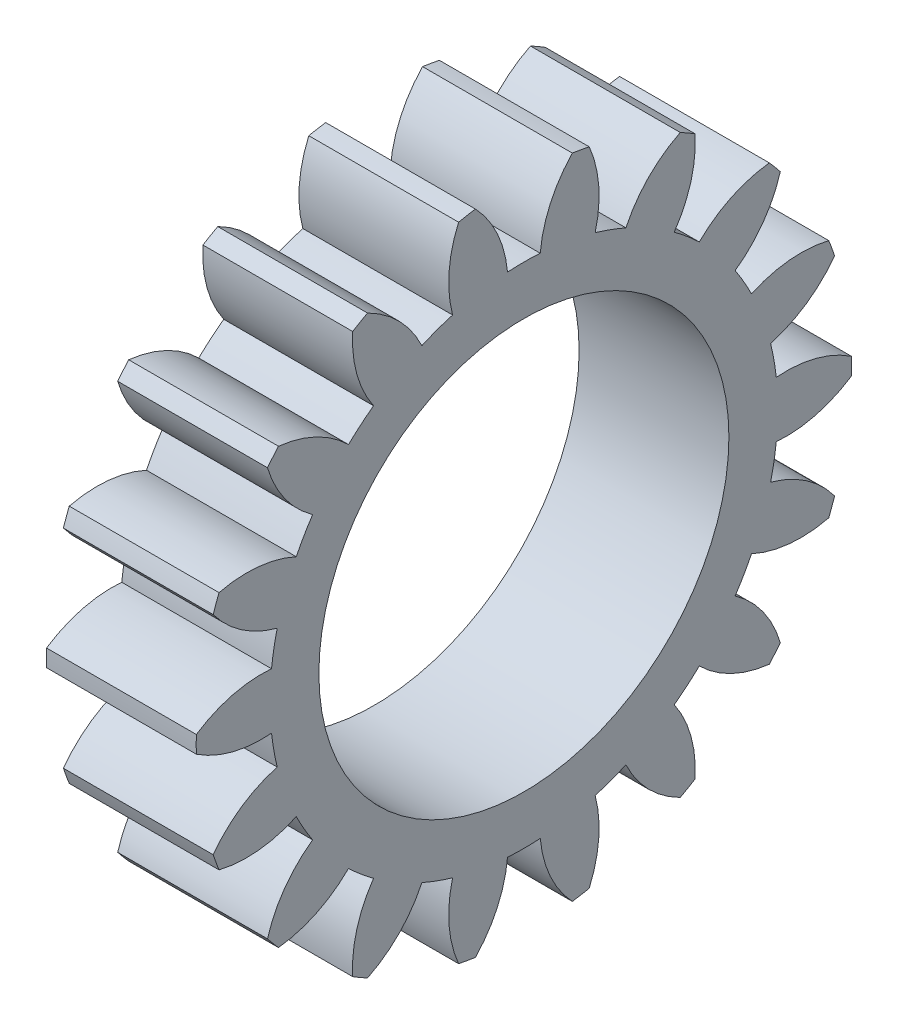
SolidWorks part; units mm, degrees
material "PLA personnalisé"
ref_plane "Plane1" through (0, 0, 0) normal (0, 0, 1) x (1, 0, 0)
ref_plane "Plane2" through (0, 0, 0) normal (0, 1, 0) x (1, 0, 0)
ref_plane "Plane3" through (0, 0, 0) normal (1, 0, 0) x (0, 0, -1)
other "Configuration Table"
sketch "HoldingSke" plane through (0, 0, 0) normal (0, 1, 0) x (1, 0, 0)
  line L0 (0, 0) -> (0.5435, -0.1766)
  line L1 (-15, 0) -> (100, 0) construction
  line L2 (0, 0) -> (-2.1039, 2.3779)
  line L3 (0, 0) -> (-11.863, 4.5341)
  line L4 (0, 0) -> (8.2133, 2.6687)
  line L5 (0, 0) -> (-46.8476, -17.4728)
  line L6 (0, 0) -> (-6.6317, -4.4744)
  line L7 (-2.1039, 2.3779) -> (8.6586, 51.2059)
  line L8 (-76.2, 54.61) -> (-74.8, 54.61)
  line L9 (-71.009, 38.7566) -> (-53.1078, 45.2721)
  line L10 (-76.2, 71.12) -> (104.1128, 71.12)
  line L11 (0, 0) -> (-8, 0)
  line L12 (-76.2, 101.6) -> (-76.147, 101.6)
  line L13 (24.9733, 27.94) -> (52.9518, 28.4284)
  line L14 (24.9733, 27.94) -> (24.9743, 27.94)
  line L15 (24.9733, 27.94) -> (100.4006, 29.5858)
  line L16 (-63.627, -1.75) -> (-12.827, -1.75)
  circle A0 centre (0, 0) radius 4
  circle A1 centre (0, 0) radius 13.5615
  circle A2 centre (0, 0) radius 37.5
  circle A3 centre (0, 0) radius 4
  dimension "MHD" = 27.123
  dimension "Hub_dia" = 75
  dimension "Bore" = 8
  dimension "MBD" = 8
  dimension "Num_teeth" = 18
  dimension "Pitch" = 0.5714
  dimension "Overall_len" = 50
  dimension "Show_teeth" = 18
  dimension "Thickness" = 8
  dimension "OAL" = 50.0001
  dimension "T_dim" = 1.4
  dimension "Ap" = 20
  dimension "H" = 19.05
  dimension "Pitch_radius" = 180.3128
  dimension "Width" = 8
  dimension "Backlash" = 0.053
  dimension "Addendum_fac" = 1
  dimension "Dedendum_fac" = 1.25
  dimension "Clearance_fac" = 0.25
  dimension "Dedendum_add" = 0.001
  dimension "Module" = 1.75
sketch "BasProSke" plane through (0, 0, 0) normal (0, 1, 0) x (1, 0, 0)
  line L0 (-10, 0) -> (60, 0) construction
  line L1 (0, 0) -> (0, 17.5)
  line L2 (0, 0) -> (8, 0)
  line L3 (8, 0) -> (8, 17.5)
  line L4 (8, 17.5) -> (0, 17.5)
  dimension "Thickness" = 8
  dimension "Diameter" = 35
revolve "Base-Revolve" add sketch "BasProSke" angle 360 about L0
sketch "TooCutSke" plane through (0, 0, 0) normal (1, 0, 0) x (0, 0, -1)
  line L1 (0, 0) -> (0, 107) construction
  line L2 (0, 0) -> (-1.4654, 15.6817) construction
  line L3 (0, 0) -> (-5.4518, 30.9188) construction
  line L4 (-1.4654, 15.6817) -> (-2.7259, 15.4594) construction
  arc A0 (0.8733, 13.5334) -> (-0.8733, 13.5334) centre (0, 0) ccw
  arc A1 (2.6093, 17.3301) -> (-2.6093, 17.3301) centre (0, 0) ccw
  circle A2 centre (0, 0) radius 15.75 construction
  circle A3 centre (0, 0) radius 14.8002 construction
  arc A4 (-0.8733, 13.5334) -> (-2.6093, 17.3301) centre (-7.1472, 12.96) ccw
  arc A5 (2.6093, 17.3301) -> (0.8733, 13.5334) centre (7.1472, 12.96) ccw
  dimension "Root_dia" = 27.123
  dimension "Overcut_dia" = 35.0508
  dimension "Pitch_dia" = 31.5
  dimension "Base_dia" = 29.6003
  dimension "Flank_rad" = 6.3
  dimension "Half_ang" = 10
  dimension "Half_CT" = 1.28
extrude "ToothCut" cut sketch "TooCutSke" along normal through all
fillet "Breaks" [suppressed] radius 0.035
fillet "RootFillets" [suppressed] radius 0.4385
pattern_circular "TeethCuts" count 18 every 20 about axis through (-10, 0, 0) along (1, 0, 0) of "ToothCut", "RootFillets", "Breaks"
sketch "HubNeaOneSke" plane through (0, 0, 0) normal (-1, 0, 0) x (0, 0, 1)
  circle A0 centre (0, 0) radius 13.5615
  dimension "Diameter" = 27.123
extrude "HubNearOne" [suppressed] add sketch "HubNeaOneSke" along normal blind 42.0001
sketch "HubNeaBotSke" plane through (0, 0, 0) normal (-1, 0, 0) x (0, 0, 1)
  circle A0 centre (0, 0) radius 13.5615
  dimension "Diameter" = 27.123
extrude "HubNearBoth" [suppressed] add sketch "HubNeaBotSke" along normal blind 21
ref_plane "FarPln" through (8, 0, 0) normal (1, 0, 0) x (0, 0, -1)
sketch "HubFarSke" plane through (8, 0, 0) normal (1, 0, 0) x (0, 0, -1)
  circle A0 centre (0, 0) radius 13.5615
  dimension "Diameter" = 27.123
extrude "HubFar" [suppressed] add sketch "HubFarSke" along normal blind 21
sketch "BorSke" plane through (0, 0, 0) normal (1, 0, 0) x (0, 0, -1)
  circle A0 centre (0, 0) radius 4
  dimension "Diameter" = 8
extrude "Bore" cut sketch "BorSke" along normal mid plane 100.0001
sketch "KeySke" plane through (0, 0, 0) normal (1, 0, 0) x (0, 0, -1)
  line L0 (-1.5, 0) -> (-1.5, 5.4)
  line L1 (-1.5, 5.4) -> (1.5, 5.4)
  line L2 (1.5, 5.4) -> (1.5, 0)
  line L3 (0, 0) -> (0, 34) construction
  line L4 (-1.5, 0) -> (1.5, 0)
  dimension "Offset" = 5.4
  dimension "Width" = 3
extrude "Keyway" [suppressed] cut sketch "KeySke" along normal mid plane 100.0001
pattern_circular "Keyway2" [suppressed] count 2 every 90 about axis through (-10, 0, 0) along (1, 0, 0)
sketch "Esquisse1" plane through (8, 0, 0) normal (1, 0, 0) x (0, 0, -1)
  circle A0 centre (0, 0) radius 10.95
  dimension "D1" = 21.9
extrude "Enlèv. mat.-Extru.1" cut sketch "Esquisse1" against normal blind 10
equation "' \"Module@HoldingSke\" = 6.35"
equation "' \"Num_teeth@HoldingSke\" = 12"
equation "' \"Ap@HoldingSke\" =  20"
equation "' \"Ap@HoldingSke\" = 20"
equation "' \"Width@HoldingSke\" = 0.5 * 25.4"
equation "' \"Hub_dia@HoldingSke\"= 1 * 25.4"
equation "' \"Hub_dia@HoldingSke\" = 1 * 25.4"
equation "' \"Overall_len@HoldingSke\" = 1.0 * 25.4"
equation "' \"Bore@HoldingSke\" = 0.75 * 25.4"
equation "' \"T_dim@HoldingSke\" = 0.1 * 25.4"
equation "' \"Width@KeySke\" = 0.25 * 25.4"
equation "' \"Show_teeth@HoldingSke\" = 13"
equation "' \"Backlash@HoldingSke\" = 0.009 * 25.4"
equation "' \"Addendum_fac@HoldingSke\" = 1.0"
equation "' \"Dedendum_fac@HoldingSke\" = 1.25"
equation "' \"Dedendum_add@HoldingSke\" = 0.00005 * 25.4"
equation "' \"Clearance_fac@HoldingSke\" = 0.25"
equation "\"Pitch@HoldingSke\" = 1 / \"Module@HoldingSke\""
equation "\"Overcut_dia@TooCutSke\" = (\"Num_teeth@HoldingSke\" + 2 * \"Addendum_fac@HoldingSke\") / \"Pitch@HoldingSke\" + 0.002 * 25.4"
equation "\"Pitch_dia@TooCutSke\" = \"Num_teeth@HoldingSke\" / \"Pitch@HoldingSke\""
equation "\"Base_dia@TooCutSke\" = \"Num_teeth@HoldingSke\" / \"Pitch@HoldingSke\" * cos((\"Ap@HoldingSke\"  * 3.14159265 / 180))"
equation "\"Root_dia@TooCutSke\" = (\"Num_teeth@HoldingSke\" + 2) / \"Pitch@HoldingSke\" - 2 * (\"Addendum_fac@HoldingSke\" + \"Dedendum_fac@HoldingSke\") / \"Pitch@HoldingSke\" - \"Dedendum_add@HoldingSke\" * 2"
equation "\"Half_ang@TooCutSke\" = 180 / \"Num_teeth@HoldingSke\""
equation "\"Half_CT@TooCutSke\" = \"Num_teeth@HoldingSke\" / \"Pitch@HoldingSke\" * sin((3.14159265 / 2 / \"Num_teeth@HoldingSke\")) / 2 - 7 * \"Backlash@HoldingSke\" / 4"
equation "\"Flank_rad@TooCutSke\" = \"Num_teeth@HoldingSke\" / \"Pitch@HoldingSke\" / 5"
equation "\"Radius@RootFillets\" = \"Clearance_fac@HoldingSke\" / \"Pitch@HoldingSke\" + \"Dedendum_add@HoldingSke\""
equation "\"Break_rad@Breaks\" = 0.02 / \"Pitch@HoldingSke\""
equation "\"Thickness@HoldingSke\" = \"Width@HoldingSke\""
equation "\"OAL@HoldingSke\" = \"Thickness@HoldingSke\""
equation "\"MHD@HoldingSke\" = (\"Num_teeth@HoldingSke\" + 2) / \"Pitch@HoldingSke\" - 2 * (\"Addendum_fac@HoldingSke\" + \"Dedendum_fac@HoldingSke\")  / \"Pitch@HoldingSke\" - \"Dedendum_add@HoldingSke\" * 2"
equation "\"MBD@HoldingSke\" = (\"Num_teeth@HoldingSke\" + 2) / \"Pitch@HoldingSke\" - 2 * (\"Addendum_fac@HoldingSke\" + \"Dedendum_fac@HoldingSke\")  / \"Pitch@HoldingSke\" - \"Dedendum_add@HoldingSke\" * 2 - 0.002 * 25.4"
equation "\"MHD@HoldingSke\" = ((sgn( \"MHD@HoldingSke\" - \"Hub_dia@HoldingSke\" )-1)*( \"MHD@HoldingSke\" - \"Hub_dia@HoldingSke\" ))/-2+ \"Hub_dia@HoldingSke\""
equation "\"MBD@HoldingSke\" = ((sgn( \"MBD@HoldingSke\" - \"Bore@HoldingSke\" )-1)*( \"MBD@HoldingSke\" - \"Bore@HoldingSke\" ))/-2+ \"Bore@HoldingSke\""
equation "\"OAL@HoldingSke\" = ((sgn( \"OAL@HoldingSke\" - \"Overall_len@HoldingSke\" )+1)*( \"OAL@HoldingSke\" - \"Overall_len@HoldingSke\" ))/2 + \"Overall_len@HoldingSke\" + 0.000002 * 25.4"
equation "\"Num_teeth@TeethCuts\" = int( \"Show_teeth@HoldingSke\" ) + 1"
equation "\"Num_teeth@TeethCuts\" = ((sgn( \"Num_teeth@TeethCuts\" - \"Num_teeth@HoldingSke\" )-1)*( \"Num_teeth@TeethCuts\" - \"Num_teeth@HoldingSke\" ))/-2+ \"Num_teeth@HoldingSke\""
equation "\"Num_teeth@TeethCuts\" = ((sgn( \"Num_teeth@TeethCuts\" - 2.0)+1)*( \"Num_teeth@TeethCuts\" - 2.0))/2 +2.0"
equation "\"Angle@TeethCuts\" = 360.0 / \"Num_teeth@HoldingSke\""
equation "\"Diameter@BasProSke\" = (\"Num_teeth@HoldingSke\" + 2 * \"Addendum_fac@HoldingSke\") / \"Pitch@HoldingSke\""
equation "\"Thickness@BasProSke\"  = \"Thickness@HoldingSke\""
equation "' \"Fillet_rad@BasProSke\" =  \"Thickness@HoldingSke\" * 0.05"
equation "' \"Fillet_rad@BasProSke\" = \"Thickness@HoldingSke\" * 0.05"
equation "\"MHD@HoldingSke\" = ((sgn( \"MHD@HoldingSke\" - \"Root_dia@TooCutSke\" )-1)*( \"MHD@HoldingSke\" - \"Root_dia@TooCutSke\" ))/-2+ \"Root_dia@TooCutSke\""
equation "\"Diameter@HubNeaOneSke\" = \"MHD@HoldingSke\""
equation "\"Length@HubNearOne\" = \"OAL@HoldingSke\" - \"Thickness@BasProSke\""
equation "\"Diameter@HubNeaBotSke\" = \"MHD@HoldingSke\""
equation "\"Length@HubNearBoth\" = ( \"OAL@HoldingSke\" - \"Thickness@BasProSke\" ) / 2.0"
equation "\"Thickness@FarPln\" = \"Thickness@BasProSke\""
equation "\"Diameter@HubFarSke\" = \"MHD@HoldingSke\""
equation "\"Length@HubFar\" = ( \"OAL@HoldingSke\" - \"Thickness@BasProSke\" ) / 2.0"
equation "\"Diameter@BorSke\" = \"MBD@HoldingSke\""
equation "\"D1@Bore\" = \"OAL@HoldingSke\" * 2.0"
equation "\"D1@Keyway\" = \"OAL@HoldingSke\" * 2.0"
equation "\"Offset@KeySke\" = \"T_dim@HoldingSke\" + \"MBD@HoldingSke\" / 2.0"
